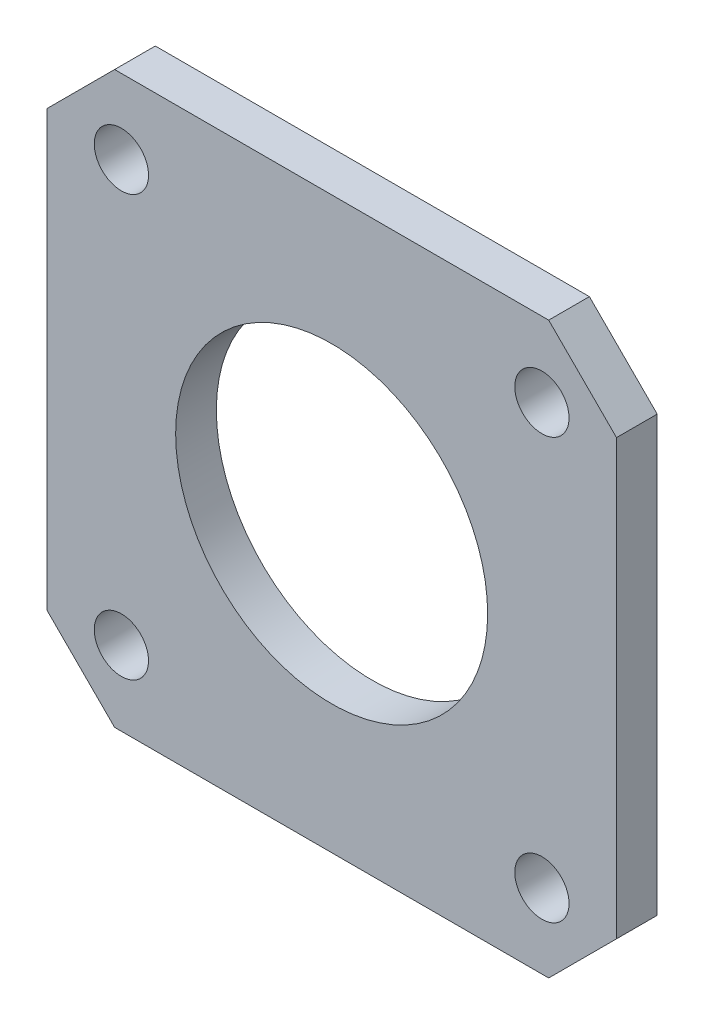
SolidWorks part; units mm, degrees
ref_plane "Piano frontale" through (0, 0, 0) normal (0, 0, 1) x (1, 0, 0)
ref_plane "Piano superiore" through (0, 0, 0) normal (0, 1, 0) x (1, 0, 0)
ref_plane "Piano destro" through (0, 0, 0) normal (1, 0, 0) x (0, 0, -1)
sketch "Schizzo1" plane through (0, 0, 0) normal (0, 0, 1) x (1, 0, 0)
  line L0 (21, 0) -> (21, 42) construction
  line L1 (5, 0) -> (37, 0)
  line L2 (0, 5) -> (0, 37)
  line L3 (5, 42) -> (37, 42)
  line L4 (42, 5) -> (42, 37)
  line L5 (5.5, 48.5694) -> (5.5, -41.0972) construction
  line L6 (-12.5669, 36.5) -> (58.9852, 36.5) construction
  line L7 (21, 21) -> (-65.3253, 21) construction
  line L8 (0, 37) -> (5, 42)
  line L9 (5, 0) -> (0, 5)
  line L10 (37, 0) -> (42, 5)
  line L11 (42, 37) -> (37, 42)
  circle A0 centre (21, 21) radius 11.5
  circle A1 centre (5.5, 36.5) radius 2
  circle A2 centre (5.5, 5.5) radius 2
  circle A3 centre (36.5, 5.5) radius 2
  circle A4 centre (36.5, 36.5) radius 2
  point P0 (0, 0)
  point P1 (42, 42)
  point P2 (0, 42)
  point P3 (42, 0)
  point P13 (5.5, 36.5)
  point P15 (5.5, 5.5)
  point P17 (36.5, 5.5)
  point P18 (36.5, 36.5)
  dimension "D3" = 23
  dimension "D6" = 4
  dimension "D1" = 42
  dimension "D2" = 42
  dimension "D4" = 15.5
  dimension "D5" = 15.5
extrude "Estrusione-Estrusione1" add sketch "Schizzo1" against normal blind 3
